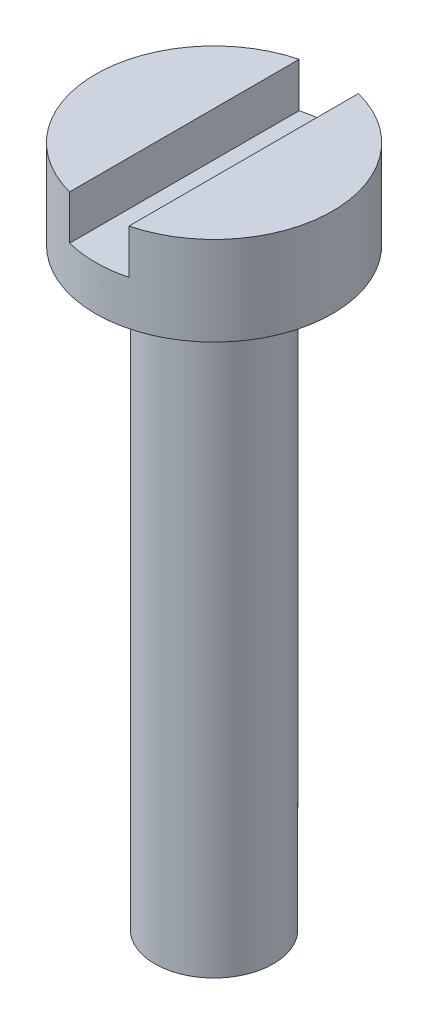
SolidWorks part; units mm, degrees
ref_plane "Front Plane" through (0, 0, 0) normal (0, 0, 1) x (1, 0, 0)
ref_plane "Top Plane" through (0, 0, 0) normal (0, 1, 0) x (1, 0, 0)
ref_plane "Right Plane" through (0, 0, 0) normal (1, 0, 0) x (0, 0, -1)
sketch "Sketch1" plane through (0, 0, 0) normal (0, 1, 0) x (1, 0, 0)
  circle A0 centre (0, 0) radius 4
extrude "Extrude1" add sketch "Sketch1" along normal blind 3
sketch "Sketch2" plane through (0, 3, 0) normal (0, 1, 0) x (-1, 0, 0)
  line L0 (0, -4) -> (0, 4) construction
  line L2 (0, 4.4012) -> (-1, 4.4012)
  line L3 (-1, 4.4012) -> (-1, -5.0783)
  line L4 (-1, -5.0783) -> (1, -5.0783)
  line L5 (1, -5.0783) -> (1, 4.4012)
  line L6 (1, 4.4012) -> (0, 4.4012)
  circle A0 centre (0, 0) radius 4 construction
extrude "Cut-Extrude1" cut sketch "Sketch2" against normal blind 1.5
sketch "Sketch3" plane through (0, 0, 0) normal (0, -1, 0) x (1, 0, 0)
  circle A0 centre (0, 0) radius 2
extrude "Extrude2" add sketch "Sketch3" along normal blind 20
